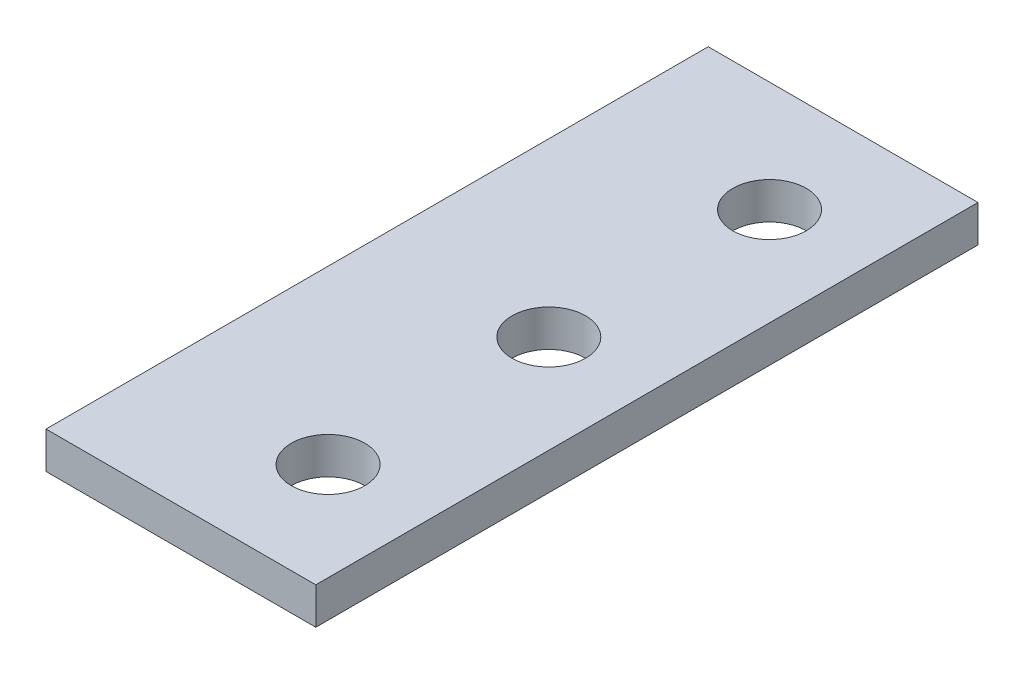
SolidWorks part; units mm, degrees
ref_plane "Front Plane" through (0, 0, 0) normal (0, 0, 1) x (1, 0, 0)
ref_plane "Top Plane" through (0, 0, 0) normal (0, 1, 0) x (1, 0, 0)
ref_plane "Right Plane" through (0, 0, 0) normal (1, 0, 0) x (0, 0, -1)
sketch "Sketch1" plane through (0, 0, 0) normal (0, 1, 0) x (1, 0, 0)
  line L1 (-31.5179, 97.5566) -> (34.4821, 97.5566)
  line L2 (-31.5179, 97.5566) -> (-31.5179, -64.4434)
  line L3 (10.4821, -64.4434) -> (34.4821, -64.4434)
  line L4 (34.4821, -40.4434) -> (34.4821, -64.4434)
  line L6 (-31.5179, -64.4434) -> (10.4821, -64.4434)
  line L7 (34.4821, 97.5566) -> (34.4821, -40.4434)
  circle A1 centre (10.4821, -37.4434) radius 9
  circle A4 centre (10.4821, 16.5566) radius 9
  circle A5 centre (10.4821, 70.5566) radius 9
  dimension "D3" = 27
  dimension "D1" = 66
  dimension "D2" = 162
  dimension "D4" = 54
  dimension "D5" = 54
extrude "Boss-Extrude1" add sketch "Sketch1" along normal blind 9
sketch "Sketch2" plane through (0, 9, 0) normal (0, 1, 0) x (1, 0, 0)
